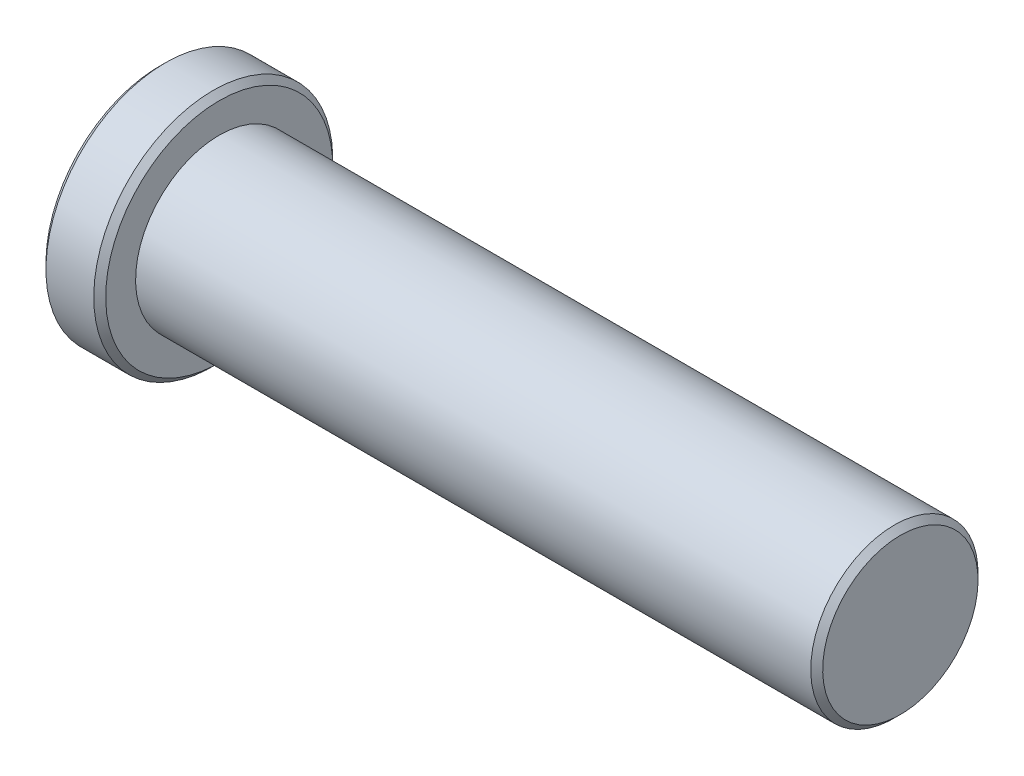
SolidWorks part; units mm, degrees
material "1.0503 (C45)"
ref_plane "Płaszczyzna XY" through (0, 0, 0) normal (0, 0, 1) x (1, 0, 0)
ref_plane "Płaszczyzna XZ" through (0, 0, 0) normal (0, 1, 0) x (1, 0, 0)
ref_plane "Płaszczyzna YZ" through (0, 0, 0) normal (1, 0, 0) x (0, 0, -1)
sketch "Szkic1" plane through (0, 0, 0) normal (0, 0, 1) x (1, 0, 0)
  line L7 (62, 0) -> (0, 0) construction
  line L13 (0, 0) -> (0, 10)
  line L14 (0, 10) -> (5, 10)
  line L15 (5, 10) -> (5, 7)
  line L16 (5, 7) -> (62, 7)
  line L17 (62, 7) -> (62, 0)
  line L18 (0, 0) -> (62, 0)
  dimension "D1" = 5
  dimension "D2" = 62
  dimension "D3" = 20
  dimension "D4" = 14
revolve "Obrót1" add sketch "Szkic1" angle 360 about L7
cosmetic thread "Oznaczenie gwintu1" parameters "D2"=12.344
chamfer "Sfazowanie1" distance 0.5 angle 45 3 edges at (62, 7, 0) (5, 10, 0) (0, 10, 0)
